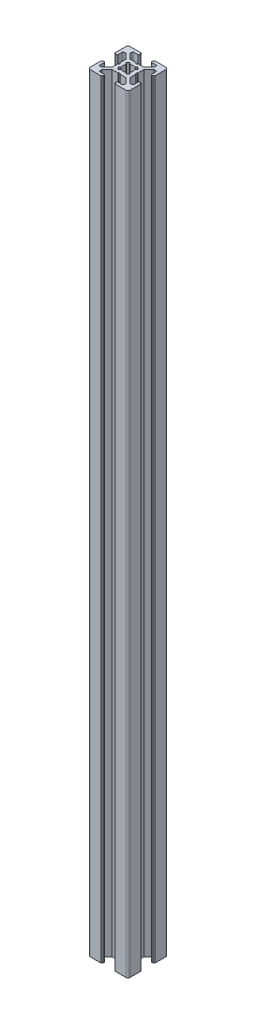
SolidWorks part; units mm, degrees
ref_plane "Front Plane" through (0, 0, 0) normal (0, 0, 1) x (1, 0, 0)
ref_plane "Top Plane" through (0, 0, 0) normal (0, 1, 0) x (1, 0, 0)
ref_plane "Right Plane" through (0, 0, 0) normal (1, 0, 0) x (0, 0, -1)
sketch "Sketch3" plane through (0, 0, 0) normal (0, 1, 0) x (1, 0, 0)
  line L0 (7, 20) -> (7, 18.5)
  line L1 (0, 0) -> (20, 0)
  line L2 (0, 0) -> (0, 20)
  line L3 (0, 20) -> (20, 20)
  line L4 (20, 0) -> (20, 20)
  line L5 (7, 18.5) -> (4, 18.5)
  line L6 (4, 18.5) -> (4, 17)
  line L7 (4, 17) -> (6.5, 14.5)
  line L8 (6.5, 14.5) -> (13.5, 14.5)
  line L9 (13.5, 14.5) -> (16, 17)
  line L10 (16, 17) -> (16, 18.5)
  line L11 (16, 18.5) -> (13, 18.5)
  line L12 (13, 18.5) -> (13, 20)
  line L13 (13, 20) -> (7, 20)
  line L14 (9.5, 14.5) -> (10, 14)
  line L15 (10, 14) -> (10.5, 14.5)
  line L16 (10.5, 14.5) -> (9.5, 14.5)
  line L17 (13, 19.5) -> (13, 20)
  line L18 (13.5, 20) -> (13, 20)
  line L19 (7, 19.5) -> (7, 20)
  line L20 (6.5, 20) -> (7, 20)
  line L21 (0, 13) -> (1.5, 13)
  line L22 (1.5, 13) -> (1.5, 16)
  line L23 (1.5, 16) -> (3, 16)
  line L24 (3, 16) -> (5.5, 13.5)
  line L25 (5.5, 13.5) -> (5.5, 6.5)
  line L26 (5.5, 6.5) -> (3, 4)
  line L27 (3, 4) -> (1.5, 4)
  line L28 (1.5, 4) -> (1.5, 7)
  line L29 (1.5, 7) -> (0, 7)
  line L30 (0, 7) -> (0, 13)
  line L31 (5.5, 10.5) -> (5.5, 9.5)
  line L32 (5.5, 9.5) -> (6, 10)
  line L33 (6, 10) -> (5.5, 10.5)
  line L34 (0.5, 13) -> (0, 13)
  line L35 (0, 13.5) -> (0, 13)
  line L36 (0, 6.5) -> (0, 7)
  line L37 (0.5, 7) -> (0, 7)
  line L38 (10, 20) -> (10, 0) construction
  line L39 (20, 10) -> (0, 10) construction
  line L40 (10, 6) -> (10.5, 5.5)
  line L41 (9.5, 5.5) -> (10, 6)
  line L42 (10.5, 5.5) -> (9.5, 5.5)
  line L43 (13.5, 0) -> (13, 0)
  line L44 (13, 0.5) -> (13, 0)
  line L45 (6.5, 0) -> (7, 0)
  line L46 (7, 0.5) -> (7, 0)
  line L47 (13, 1.5) -> (13, 0)
  line L48 (16, 1.5) -> (13, 1.5)
  line L49 (16, 3) -> (16, 1.5)
  line L50 (13.5, 5.5) -> (16, 3)
  line L51 (6.5, 5.5) -> (13.5, 5.5)
  line L52 (4, 3) -> (6.5, 5.5)
  line L53 (4, 1.5) -> (4, 3)
  line L54 (7, 1.5) -> (4, 1.5)
  line L55 (7, 0) -> (7, 1.5)
  line L56 (13, 0) -> (7, 0)
  line L57 (14.5, 9.5) -> (14, 10)
  line L58 (14.5, 10.5) -> (14.5, 9.5)
  line L59 (14, 10) -> (14.5, 10.5)
  line L60 (19.5, 7) -> (20, 7)
  line L61 (20, 6.5) -> (20, 7)
  line L62 (20, 13.5) -> (20, 13)
  line L63 (19.5, 13) -> (20, 13)
  line L64 (18.5, 7) -> (20, 7)
  line L65 (18.5, 4) -> (18.5, 7)
  line L66 (17, 4) -> (18.5, 4)
  line L67 (14.5, 6.5) -> (17, 4)
  line L68 (14.5, 13.5) -> (14.5, 6.5)
  line L69 (17, 16) -> (14.5, 13.5)
  line L70 (18.5, 16) -> (17, 16)
  line L71 (18.5, 13) -> (18.5, 16)
  line L72 (20, 13) -> (18.5, 13)
  line L73 (20, 7) -> (20, 13)
  arc A0 (13.5, 20) -> (13, 19.5) centre (13, 20) cw
  arc A1 (6.5, 20) -> (7, 19.5) centre (7, 20) ccw
  arc A2 (0.5, 13) -> (0, 13.5) centre (0, 13) ccw
  arc A3 (0.5, 7) -> (0, 6.5) centre (0, 7) cw
  arc A4 (13.5, 0) -> (13, 0.5) centre (13, 0) ccw
  arc A5 (6.5, 0) -> (7, 0.5) centre (7, 0) cw
  arc A6 (19.5, 7) -> (20, 6.5) centre (20, 7) ccw
  arc A7 (19.5, 13) -> (20, 13.5) centre (20, 13) cw
  point P7 (10, 14.5)
  point P16 (10, 20)
  point P26 (5.5, 10)
  point P35 (0, 10)
  dimension "D16" = 0.5
  dimension "D17" = 0.5
  dimension "D28" = 0.5
  dimension "D29" = 0.5
  dimension "D1" = 20
  dimension "D2" = 20
  dimension "D3" = 7
  dimension "D4" = 7
  dimension "D5" = 1.5
  dimension "D6" = 1.5
  dimension "D7" = 3
  dimension "D8" = 3
  dimension "D9" = 1.5
  dimension "D10" = 1.5
  dimension "D11" = 7
  dimension "D12" = 5.5
  dimension "D13" = 0.5
  dimension "D14" = 0.5
  dimension "D15" = 0.5
  dimension "D18" = 7
  dimension "D19" = 7
  dimension "D20" = 1.5
  dimension "D21" = 1.5
  dimension "D22" = 3
  dimension "D23" = 7
  dimension "D24" = 5.5
  dimension "D25" = 0.5
  dimension "D26" = 0.5
  dimension "D27" = 0.5
extrude "Boss-Extrude1" add sketch "Sketch3" along normal blind 385 contours L72 A7 L4 L3 A0 L12 L11 L10 L9 L8 L15 L14 L7 L6 L5 L0 A1 L2 A2 L21 L22 L23 L24 L25 L33 L32 L26 L27 L28 L29 A3 L1 A5 L55 L54 L53 L52 L51 L41 L40 L50 L49 L48 L47 A4
fillet "Fillet1" radius 1 4 edges at (0, 192.5, 0) (20, 192.5, 0) (20, 192.5, -20) (0, 192.5, -20)
sketch "Sketch4" plane through (0, 385, 0) normal (0, 1, 0) x (1, 0, 0)
  line L0 (13.5, 14.5) -> (5.5, 6.5) construction
  line L1 (14.5, 13.5) -> (6.5, 5.5) construction
  line L2 (10.5, 14.5) -> (14.5, 10.5) construction
  line L3 (12, 13) -> (13, 12)
  line L4 (13, 12) -> (8, 7)
  line L5 (8, 7) -> (7, 8)
  line L6 (7, 8) -> (12, 13)
  line L7 (13.5, 14.5) -> (16, 17) construction
  line L8 (17, 16) -> (14.5, 13.5) construction
  line L9 (5.5, 9.5) -> (9.5, 5.5) construction
  line L10 (5.5, 10.5) -> (9.5, 14.5) construction
  line L11 (14.5, 9.5) -> (10.5, 5.5) construction
  line L12 (6.5, 14.5) -> (14.5, 6.5) construction
  line L13 (5.5, 13.5) -> (13.5, 5.5) construction
  line L14 (7, 12) -> (8, 13)
  line L15 (8, 13) -> (13, 8)
  line L16 (13, 8) -> (12, 7)
  line L17 (12, 7) -> (7, 12)
  line L18 (4, 17) -> (6.5, 14.5) construction
  line L19 (3, 16) -> (5.5, 13.5) construction
  line L20 (20, 10) -> (0, 10) construction
  circle A0 centre (10, 10) radius 2.5
  dimension "D1" = 5
extrude "Cut-Extrude1" cut sketch "Sketch4" against normal through all contours L6 A0 L15 | L4 A0 L6 L15 | L15 A0 L17 L6 | L17 L4 L15 L6 | L17 A0 L6 | L6 A0 L4 L17 | L4 A0 L17 | L17 A0 L15 L4 | L15 A0 L4 | A0 L6 L5 L4 | A0 L17 L16 L15 | A0 L4 L3 L6 | A0 L15 L14 L17
fillet "Fillet2" radius 0.5 24 edges at (1.5, 192.5, -16) (1.5, 192.5, -13) (5.5, 192.5, -10.5) (5.5, 192.5, -9.5) (1.5, 192.5, -7) (1.5, 192.5, -4) (4, 192.5, -1.5) (7, 192.5, -1.5) (9.5, 192.5, -5.5) (10.5, 192.5, -5.5) (13, 192.5, -1.5) (16, 192.5, -1.5) (18.5, 192.5, -4) (18.5, 192.5, -7) (18.5, 192.5, -13) (18.5, 192.5, -16) (14.5, 192.5, -9.5) (14.5, 192.5, -10.5) (10.5, 192.5, -14.5) (9.5, 192.5, -14.5) (16, 192.5, -18.5) (13, 192.5, -18.5) (7, 192.5, -18.5) (4, 192.5, -18.5)
fillet "Fillet3" radius 0.25 8 edges at (13, 192.5, -8) (12, 192.5, -7) (13, 192.5, -12) (12, 192.5, -13) (8, 192.5, -13) (7, 192.5, -12) (7, 192.5, -8) (8, 192.5, -7)
